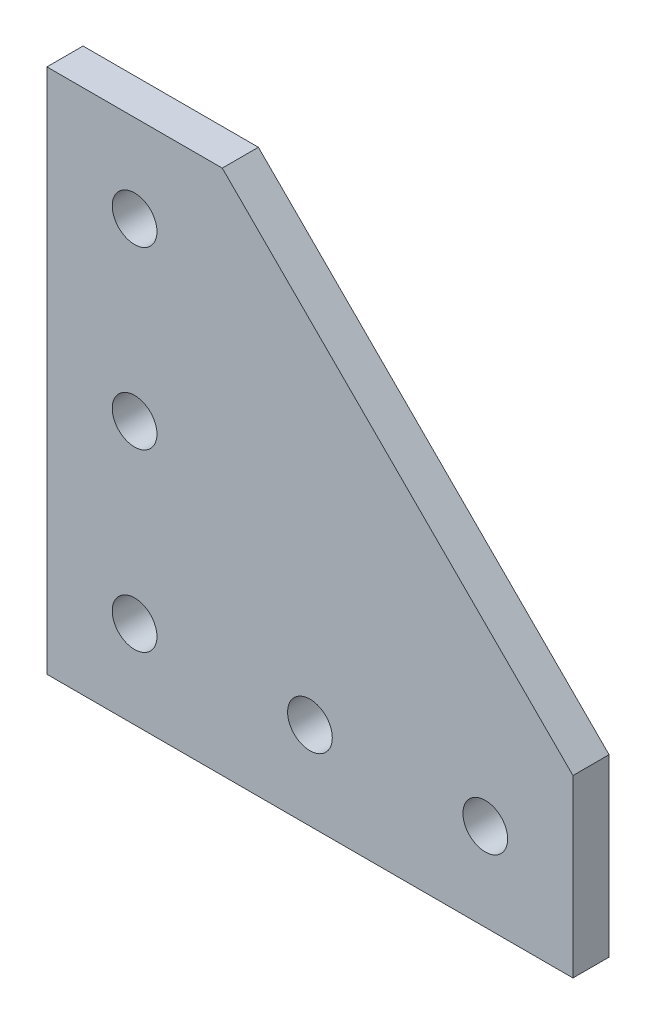
SolidWorks part; units mm, degrees
material "1060 Alloy"
ref_plane "Front Plane" through (0, 0, 0) normal (0, 0, 1) x (1, 0, 0)
ref_plane "Top Plane" through (0, 0, 0) normal (0, 1, 0) x (1, 0, 0)
ref_plane "Right Plane" through (0, 0, 0) normal (1, 0, 0) x (0, 0, -1)
sketch "Sketch1" plane through (0, 0, 0) normal (0, 0, 1) x (1, 0, 0)
  line L0 (0, 0) -> (0, 60)
  line L1 (0, 60) -> (20, 60)
  line L2 (0, 0) -> (60, 0)
  line L3 (60, 0) -> (60, 20)
  line L4 (20, 60) -> (60, 20)
  dimension "D1" = 20
  dimension "D2" = 60
  dimension "D3" = 60
  dimension "D4" = 20
  dimension "D5" = 56.5685
extrude "Boss-Extrude1" add sketch "Sketch1" along normal blind 4.12
sketch "Sketch2" plane through (0, 0, 4.12) normal (0, 0, 1) x (1, 0, 0)
  line L0 (0, 0) -> (60, 0) construction
  line L1 (0, 60) -> (0, 0) construction
  circle A0 centre (10, 10) radius 2.55
  circle A1 centre (30, 10) radius 2.55
  circle A2 centre (50, 10) radius 2.55
  circle A3 centre (10, 30) radius 2.55
  circle A4 centre (10, 50) radius 2.55
  point P7 (0, 0)
  point P15 (0, 0)
  dimension "D1" = 5.1
  dimension "D2" = 10
  dimension "D3" = 10
  dimension "D6" = 20
  dimension "D7" = 20
  dimension "D4" = 3
  dimension "D5" = 3
extrude "Cut-Extrude1" cut sketch "Sketch2" against normal through all
